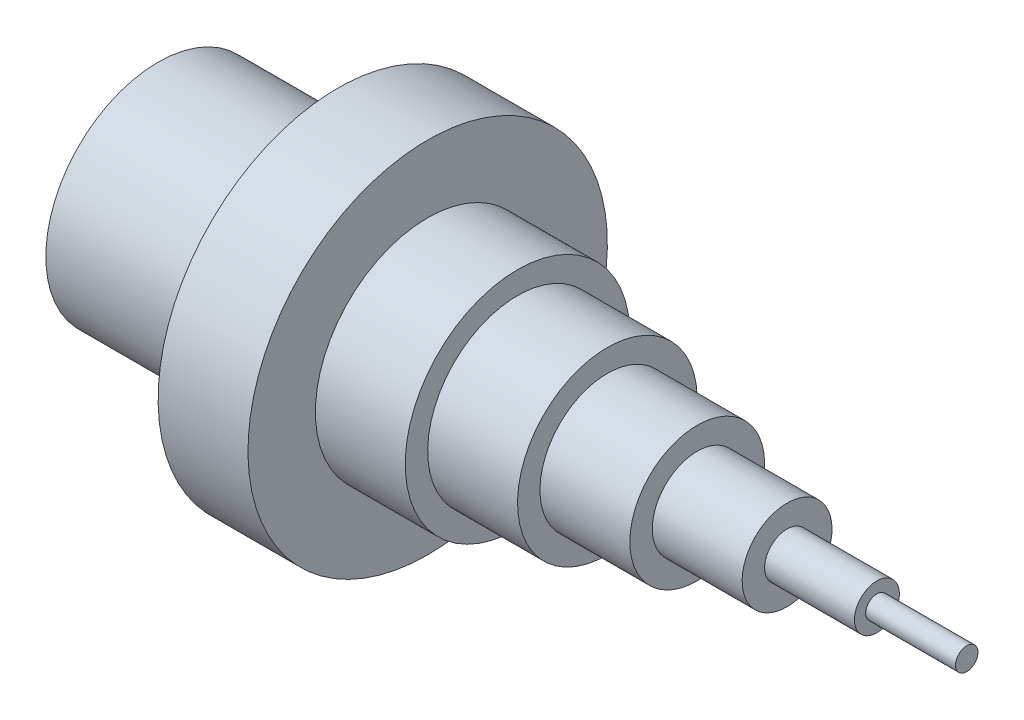
SolidWorks part; units mm, degrees
ref_plane "Front Plane" through (0, 0, 0) normal (0, 0, 1) x (1, 0, 0)
ref_plane "Top Plane" through (0, 0, 0) normal (0, 1, 0) x (1, 0, 0)
ref_plane "Right Plane" through (0, 0, 0) normal (1, 0, 0) x (0, 0, -1)
sketch "Sketch2" plane through (0, 0, 0) normal (0, 0, 1) x (1, 0, 0)
  line L0 (60, 40) -> (60, 25)
  line L1 (60, 25) -> (80, 25)
  line L2 (80, 25) -> (80, 20)
  line L3 (80, 20) -> (100, 20)
  line L4 (100, 20) -> (100, 15)
  line L5 (100, 15) -> (120, 15)
  line L6 (120, 15) -> (120, 10)
  line L7 (120, 10) -> (140, 10)
  line L8 (140, 10) -> (140, 5)
  line L9 (140, 5) -> (160, 5)
  line L10 (160, 5) -> (160, 2.5)
  line L11 (160, 2.5) -> (180, 2.5)
  line L12 (180, 2.5) -> (180, 0)
  line L13 (0, 0) -> (212.8574, 0) construction
  line L14 (0, 0) -> (180, 0)
  line L15 (0, 0) -> (0, 25)
  line L16 (0, 25) -> (40, 25)
  line L17 (40, 25) -> (40, 40)
  line L18 (40, 40) -> (60, 40)
  dimension "D2" = 5
  dimension "D3" = 10
  dimension "D4" = 20
  dimension "D5" = 30
  dimension "D6" = 40
  dimension "D7" = 50
  dimension "D8" = 50
  dimension "D9" = 180
  dimension "D10" = 20
  dimension "D11" = 20
  dimension "D12" = 20
  dimension "D13" = 80
revolve "Revolve1" add sketch "Sketch2" angle 360 about L14
sketch "Sketch3" plane through (0, 0, 0) normal (-1, 0, 0) x (0, 0, 1)
  circle A0 centre (0, 0) radius 20
  dimension "D1" = 40
extrude "Cut-Extrude2" cut sketch "Sketch3" against normal blind 40
